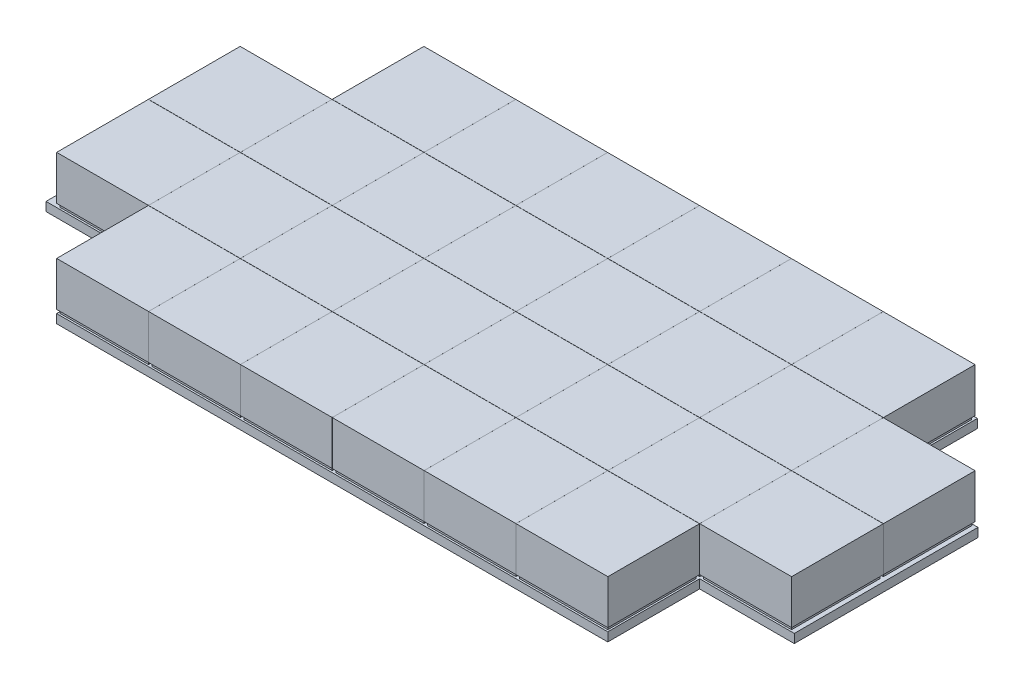
SolidWorks part; units mm, degrees
ref_plane "Front Plane" through (0, 0, 0) normal (0, 0, 1) x (1, 0, 0)
ref_plane "Top Plane" through (0, 0, 0) normal (0, 1, 0) x (1, 0, 0)
ref_plane "Right Plane" through (0, 0, 0) normal (1, 0, 0) x (0, 0, -1)
sketch "Sketch1" plane through (0, 0, 0) normal (0, 1, 0) x (1, 0, 0)
  line L1 (-240, -135) -> (240, -135)
  line L2 (-240, -135) -> (-240, 135)
  line L3 (-240, 135) -> (240, 135)
  line L4 (240, -135) -> (240, 135)
  line L5 (-240, -135) -> (240, 135) construction
  line L6 (-240, 135) -> (240, -135) construction
  point P0 (0, 0)
  dimension "D1" = 480
  dimension "D2" = 270
extrude "Boss-Extrude1" add sketch "Sketch1" along normal blind 5
sketch "Sketch2" plane through (0, 5, 0) normal (0, 1, 0) x (1, 0, 0)
  line L0 (0, 0) -> (0, -135) construction
  line L1 (-240, -135) -> (240, -135) construction
  line L3 (-25, -80) -> (25, -80)
  line L4 (-25, -80) -> (-25, -130)
  line L5 (-25, -130) -> (25, -130)
  line L6 (25, -80) -> (25, -130)
  line L7 (-25, -80) -> (25, -130) construction
  line L8 (-25, -130) -> (25, -80) construction
  point P5 (0, -105)
  dimension "D1" = 50
  dimension "D2" = 50
  dimension "D3" = 5
extrude "Boss-Extrude3" add sketch "Sketch2" along normal blind 2
pattern_linear "LPattern1" count 5 spacing 52 along (0, 0, -1) of "Boss-Extrude3"
sketch "Sketch3" plane through (0, 7, 0) normal (0, 1, 0) x (1, 0, 0)
  line L0 (0, 0) -> (0, -130) construction
  line L1 (-25, -130) -> (25, -130) construction
  line L3 (-26, -79.1) -> (26, -79.1)
  line L4 (-26, -79.1) -> (-26, -131)
  line L5 (-26, -131) -> (26, -131)
  line L6 (26, -79.1) -> (26, -131)
  line L7 (-26, -79.1) -> (26, -131) construction
  line L8 (-26, -131) -> (26, -79.1) construction
  line L9 (-240, -135) -> (240, -135) construction
  point P5 (0, -105.05)
  dimension "D1" = 52
  dimension "D2" = 51.9
  dimension "D3" = 4
extrude "Boss-Extrude8" add sketch "Sketch3" along normal blind 25
pattern_linear "LPattern5" count 5 spacing 52 along (0, 0, -1) of "Boss-Extrude8"
pattern_linear "LPattern6" count 4 spacing 52.01 along (1, 0, 0) count 5 spacing 52.01 along (-1, 0, 0) of "Boss-Extrude3", "LPattern1", "Boss-Extrude8", "LPattern5"
sketch "Sketch4" plane through (0, 5, 0) normal (0, 1, 0) x (1, 0, 0)
  line L5 (130.0253, 76.9491) -> (240, 76.9491)
  line L6 (130.0253, 76.9491) -> (130.0253, 135)
  line L7 (130.0253, 135) -> (240, 135)
  line L8 (240, 76.9491) -> (240, 135)
  line L9 (-182.0345, 76.9491) -> (-240, 76.9491)
  line L10 (-182.0345, 76.9491) -> (-182.0345, 135)
  line L11 (-182.0345, 135) -> (-240, 135)
  line L12 (-240, 76.9491) -> (-240, 135)
  line L17 (-182.0345, -27.0593) -> (-240, -27.0593)
  line L18 (-182.0345, -27.0593) -> (-182.0345, -135)
  line L19 (-182.0345, -135) -> (-240, -135)
  line L20 (-240, -27.0593) -> (-240, -135)
  line L21 (130.0253, -27.0593) -> (240, -27.0593)
  line L22 (130.0253, -27.0593) -> (130.0253, -135)
  line L23 (130.0253, -135) -> (240, -135)
  line L24 (240, -27.0593) -> (240, -135)
extrude "Cut-Extrude1" cut sketch "Sketch4" against normal through all both and the other way through all
sketch "Sketch5" plane through (0, 5, 0) normal (0, 1, 0) x (1, 0, 0)
  line L0 (-182.0345, -27.0593) -> (-182.0345, -135) construction
  line L1 (-182.0345, -79.0521) -> (130.0253, -79.0521)
  line L2 (-182.0345, -79.0521) -> (-182.0345, -135)
  line L3 (-182.0345, -135) -> (130.0253, -135)
  line L4 (130.0253, -79.0521) -> (130.0253, -135)
  line L5 (130.0253, -27.0593) -> (240, -27.0593) construction
  line L6 (240, 76.9491) -> (183.6174, 76.9491)
  line L7 (240, 76.9491) -> (240, -27.0593)
  line L8 (240, -27.0593) -> (183.6174, -27.0593)
  line L9 (183.6174, 76.9491) -> (183.6174, -27.0593)
  line L10 (130.0253, 76.9491) -> (130.0253, 135) construction
  line L11 (-182.0345, 135) -> (130.0253, 135)
  line L12 (-182.0345, 135) -> (-182.0345, 130.2098)
  line L13 (-182.0345, 130.2098) -> (130.0253, 130.2098)
  line L14 (130.0253, 135) -> (130.0253, 130.2098)
extrude "Cut-Extrude2" cut sketch "Sketch5" against normal through all both and the other way through all
